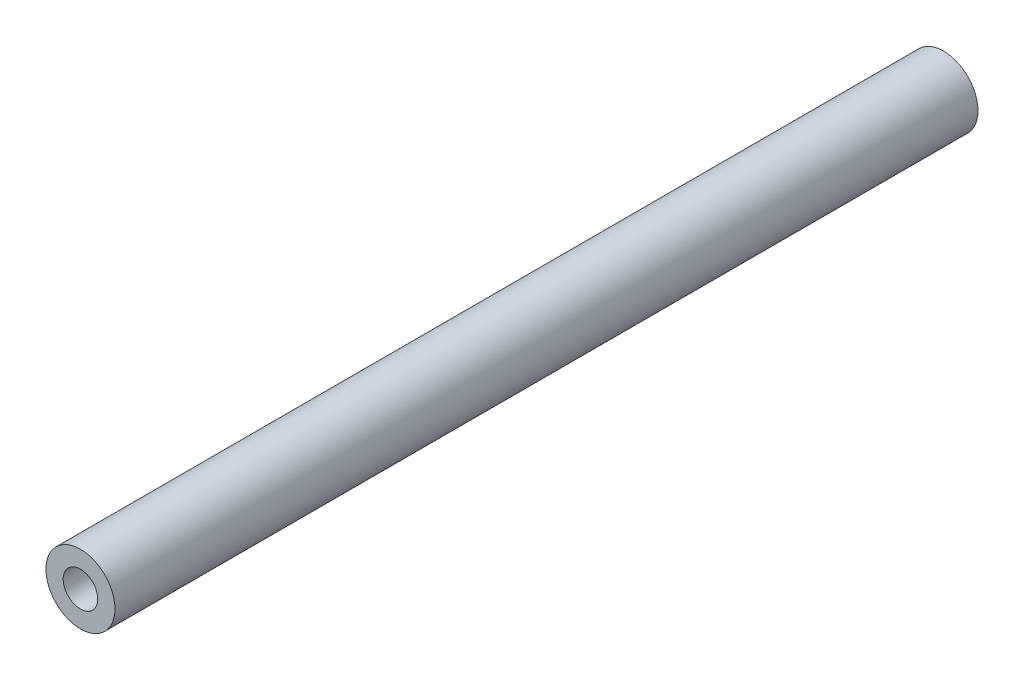
SolidWorks part; units mm, degrees
ref_plane "前视基准面" through (0, 0, 0) normal (0, 0, 1) x (1, 0, 0)
ref_plane "上视基准面" through (0, 0, 0) normal (0, 1, 0) x (1, 0, 0)
ref_plane "右视基准面" through (0, 0, 0) normal (1, 0, 0) x (0, 0, -1)
other "Configuration Table"
sketch "草图1" plane through (0, 0, 0) normal (0, 0, 1) x (1, 0, 0)
  circle A0 centre (0, 2.6536) radius 4
  circle A1 centre (0, 2.6536) radius 2
  dimension "D1" = 8
  dimension "D2" = 4
extrude "凸台-拉伸1" add sketch "草图1" along normal blind 100 contours A0 A1
